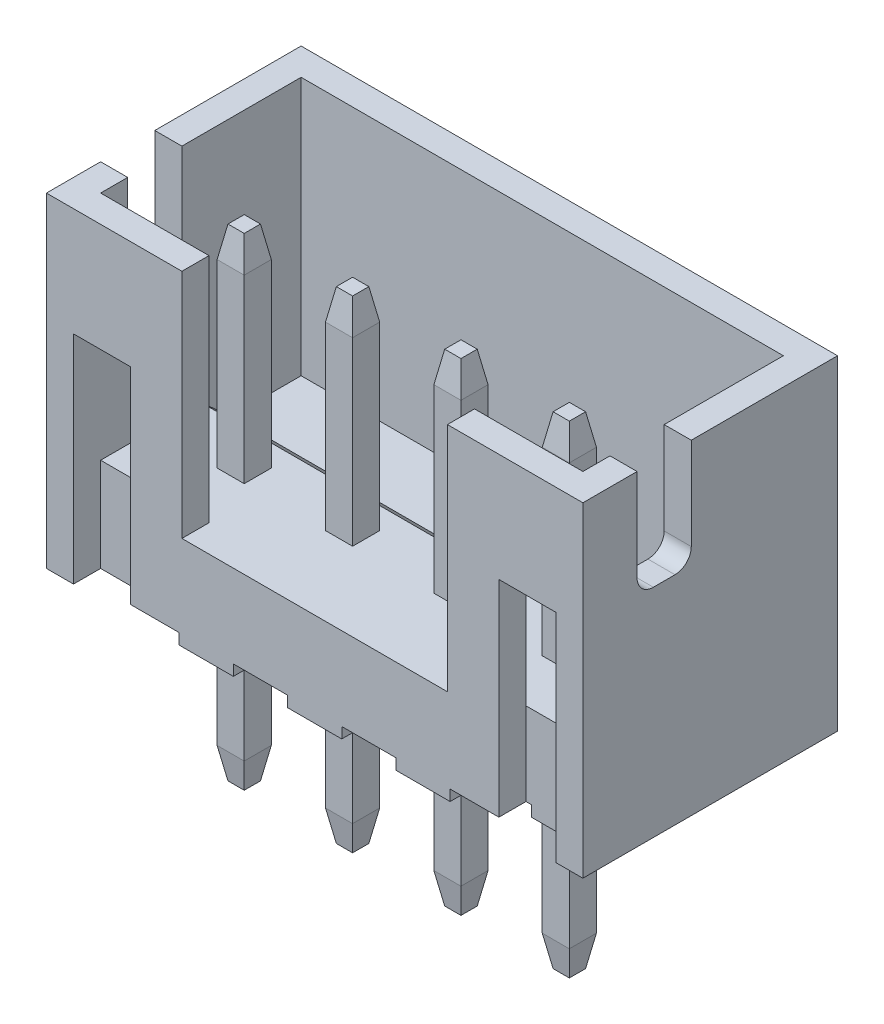
SolidWorks part; units mm, degrees
ref_plane "Спереди" through (0, 0, 0) normal (0, 0, 1) x (1, 0, 0)
ref_plane "Сверху" through (0, 0, 0) normal (0, 1, 0) x (1, 0, 0)
ref_plane "Справа" through (0, 0, 0) normal (1, 0, 0) x (0, 0, -1)
sketch "Эскиз1" plane through (0, 0, 0) normal (0, 1, 0) x (1, 0, 0)
  line L0 (0, 2.6811) -> (0, -2.5744) construction
  line L2 (0, 2.35) -> (-4.95, 2.35)
  line L3 (0, 2.35) -> (0, -2.35)
  line L4 (0, -2.35) -> (-4.95, -2.35)
  line L5 (-4.95, 2.35) -> (-4.95, -2.35)
  point P8 (0, 0)
  dimension "D1" = 4.95
  dimension "D2" = 4.7
extrude "Бобышка-Вытянуть1" add sketch "Эскиз1" along normal blind 1.73
sketch "Эскиз2" plane through (0, 1.73, 0) normal (0, 1, 0) x (1, 0, 0)
  line L0 (0, 2.35) -> (-4.95, 2.35)
  line L1 (-4.95, 2.35) -> (-4.95, -2.35)
  line L2 (-4.95, -2.35) -> (0, -2.35)
  line L3 (0, -2.35) -> (0, -1.85)
  line L4 (0, -2.35) -> (0, 2.35) construction
  line L5 (0, -1.85) -> (-4.45, -1.85)
  line L6 (-4.45, -1.85) -> (-4.45, 1.85)
  line L7 (-4.45, 1.85) -> (0, 1.85)
  line L8 (0, 1.85) -> (0, 2.35)
  dimension "D1" = 0.5
  dimension "D2" = 0.5
  dimension "D3" = 0.5
extrude "Бобышка-Вытянуть2" add sketch "Эскиз2" along normal offset from surface (4.27 mm away) 6 up to face at (-2.475, 0, 0)
sketch "Эскиз3" plane through (-4.45, 0, 0) normal (1, 0, 0) x (0, 0, -1)
  line L0 (-1.85, 6) -> (-1.85, 1.73) construction
  line L1 (-1.35, 6) -> (-0.35, 6)
  line L2 (-1.35, 6) -> (-1.35, 4.3)
  line L3 (-1.05, 4) -> (-0.65, 4)
  line L4 (-0.35, 6) -> (-0.35, 4.3)
  arc A0 (-0.65, 4) -> (-0.35, 4.3) centre (-0.65, 4.3) ccw
  arc A1 (-1.35, 4.3) -> (-1.05, 4) centre (-1.05, 4.3) ccw
  point P9 (-0.35, 4)
  point P12 (-1.35, 4)
  dimension "D4" = 0.3
  dimension "D1" = 1
  dimension "D2" = 2
  dimension "D3" = 0.5
extrude "Вырез-Вытянуть1" cut sketch "Эскиз3" against normal through all
sketch "Эскиз8" plane through (0, 0, 0) normal (1, 0, 0) x (0, 0, -1)
  line L0 (0, 1.73) -> (0.55, 1.23)
  line L1 (-1.85, 1.73) -> (1.85, 1.73) construction
  line L2 (0.55, 1.23) -> (1.85, 1.23)
  line L3 (1.85, 1.23) -> (1.85, 1.73)
  line L4 (1.85, 1.73) -> (0, 1.73)
  dimension "D1" = 0.5
  dimension "D2" = 1.3
extrude "Вырез-Вытянуть3" cut sketch "Эскиз8" against normal up to surface (4.45 mm away) up to face at (-4.45, 4.3936, 0.51)
sketch "Эскиз4" plane through (0, 0, 2.35) normal (0, 0, 1) x (1, 0, 0)
  line L0 (-4.95, 0) -> (0, 0) construction
  line L1 (-4.95, 6) -> (0, 6) construction
  line L2 (-4.45, 4) -> (-3.4, 4)
  line L3 (-2.45, 6) -> (-2.45, 1.73)
  line L4 (-2.45, 1.73) -> (0, 1.73)
  line L5 (0, 6) -> (0, 0) construction
  line L6 (0, 1.73) -> (0, 6)
  line L7 (0, 6) -> (-2.45, 6)
  line L8 (-4.95, 6) -> (-4.95, 0) construction
  line L9 (-4.45, 4) -> (-4.45, 0)
  line L10 (-4.45, 0) -> (-3.4, 0)
  line L11 (-3.4, 4) -> (-3.4, 0)
  line L12 (-4.45, 1.73) -> (0, 1.73) construction
  dimension "D5" = 4
  dimension "D1" = 2.5
  dimension "D2" = 0.5
  dimension "D3" = 1.05
extrude "Вырез-Вытянуть2" cut sketch "Эскиз4" against normal up to surface (0.5 mm away) up to face at (-2.225, 3.865, 1.85)
mirror "Зеркальное отражение1" about plane through (0, 0, 0) normal (1, 0, 0) of "Вырез-Вытянуть3", "Бобышка-Вытянуть1", "Бобышка-Вытянуть2", "Вырез-Вытянуть1", "Вырез-Вытянуть2"
ref_plane "Плоскость1" through (-3, 0, 0) normal (-1, 0, 0) x (0, 0, 1)
sketch "Эскиз9" plane through (-3, 0, 0) normal (-1, 0, 0) x (0, 0, 1)
  line L0 (2.35, 0) -> (-2.35, 0)
  line L1 (-2.35, 0) -> (-2.35, 0.5)
  line L2 (-2.35, 6) -> (-2.35, 0) construction
  line L3 (-2.35, 0.5) -> (-0.05, 0.2)
  line L4 (-0.05, 0.2) -> (2.35, 0.2)
  line L5 (2.35, 6) -> (2.35, 0) construction
  line L6 (2.35, 0.2) -> (2.35, 0)
  dimension "D1" = 0.5
  dimension "D2" = 0.2
  dimension "D3" = 2.3
extrude "Вырез-Вытянуть4" cut sketch "Эскиз9" against normal blind 0.5 and the other way blind 0.5
sketch "Эскиз5" plane through (0, 1.73, 0) normal (0, 1, 0) x (1, 0, 0)
  line L1 (-3.25, -0.4) -> (-2.75, -0.4)
  line L2 (-3.25, -0.4) -> (-3.25, -0.9)
  line L3 (-3.25, -0.9) -> (-2.75, -0.9)
  line L4 (-2.75, -0.4) -> (-2.75, -0.9)
  line L7 (-4.95, -0.35) -> (-4.95, 2.35) construction
  line L8 (-2.45, -2.35) -> (-4.95, -2.35) construction
  point P4 (-3.25, -0.65)
  point P6 (-3, -0.4)
  dimension "D1" = 0.5
  dimension "D2" = 0.5
  dimension "D3" = 1.7
  dimension "D4" = 1.95
extrude "Бобышка-Вытянуть3" add sketch "Эскиз5" along normal offset from surface 0.37 and the other way blind 5 up to face at (0, 6, -0.875)
chamfer "Фаска1" distance 0.1 angle 80 8 edges at (-3, -3.27, 0.9) (-2.75, -3.27, 0.65) (-3, -3.27, 0.4) (-3.25, -3.27, 0.65) (-2.75, 5.63, 0.65) (-3, 5.63, 0.9) (-3.25, 5.63, 0.65) (-3, 5.63, 0.4)
pattern_linear "Линейный массив1" count 4 spacing 2 along (1, 0, 0) of "Бобышка-Вытянуть3", "Фаска1", "Вырез-Вытянуть4"
equation "\"JST\"= 4"
equation "\"D1@Линейный массив1\"=\"JST\""
equation "\"D1@Эскиз1\"=0.95+1*\"JST\""
